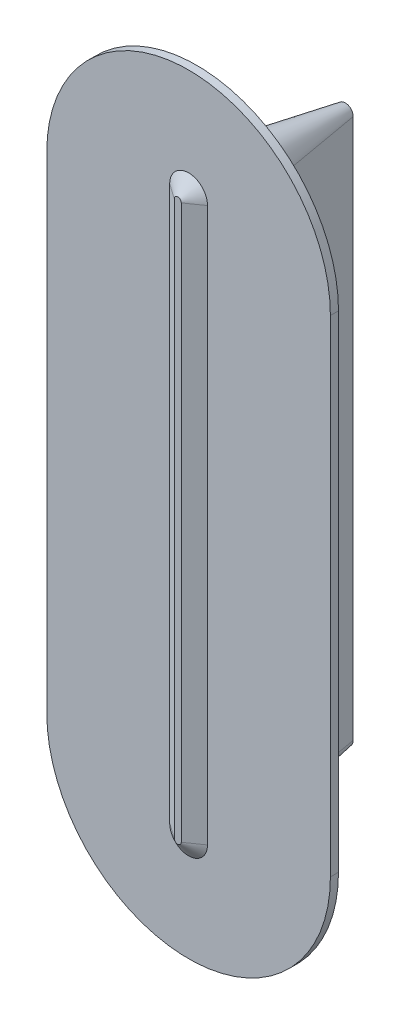
SolidWorks part; units mm, degrees
material "1060-O (SS)"
ref_plane "Front Plane" through (0, 0, 0) normal (0, 0, 1) x (1, 0, 0)
ref_plane "Top Plane" through (0, 0, 0) normal (0, 1, 0) x (1, 0, 0)
ref_plane "Right Plane" through (0, 0, 0) normal (1, 0, 0) x (0, 0, -1)
sketch "Sketch1" plane through (0, 0, 0) normal (0, 0, 1) x (1, 0, 0)
  line L0 (0, -100) -> (0, 100) construction
  line L1 (-10, -100) -> (-10, 100)
  line L2 (10, -100) -> (10, 100)
  arc A0 (-10, -100) -> (10, -100) centre (0, -100) ccw
  arc A1 (10, 100) -> (-10, 100) centre (0, 100) ccw
  point P2 (0, 0)
  dimension "D1" = 200
  dimension "D2" = 20
extrude "Boss-Extrude1" add sketch "Sketch1" along normal blind 15 and the other way blind 40 draft 10
sketch "Sketch2" plane through (0, 0, 15) normal (0, 0, 1) x (1, 0, 0)
  line L0 (0, -90) -> (0, 90) construction
  line L1 (-52.5, -90) -> (-52.5, 90)
  line L2 (52.5, -90) -> (52.5, 90)
  arc A0 (-52.5, -90) -> (52.5, -90) centre (0, -90) ccw
  arc A1 (52.5, 90) -> (-52.5, 90) centre (0, 90) ccw
  point P2 (0, 0)
  dimension "D1" = 180
  dimension "D2" = 105
extrude "Boss-Extrude2" add sketch "Sketch2" along normal blind 3
sketch "Sketch3" plane through (0, 0, 18) normal (0, 0, 1) x (1, 0, 0)
  line L0 (0, -102.5) -> (0, 102.5) construction
  line L1 (-7, -102.5) -> (-7, 102.5)
  line L2 (7, -102.5) -> (7, 102.5)
  arc A0 (-7, -102.5) -> (7, -102.5) centre (0, -102.5) ccw
  arc A1 (7, 102.5) -> (-7, 102.5) centre (0, 102.5) ccw
  point P2 (0, 0)
  dimension "D1" = 205
  dimension "D2" = 14
extrude "Boss-Extrude3" add sketch "Sketch3" along normal blind 4 draft 55
